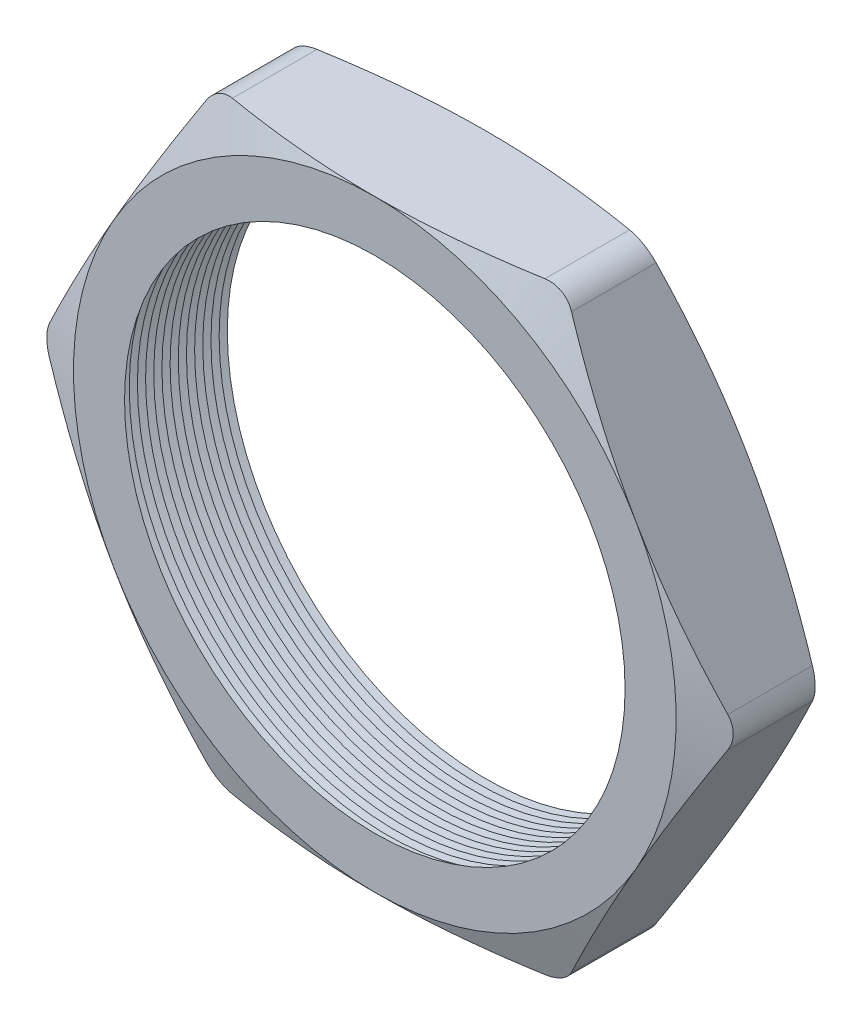
SolidWorks part; units mm, degrees
ref_plane "Front Plane" through (0, 0, 0) normal (0, 0, 1) x (1, 0, 0)
ref_plane "Top Plane" through (0, 0, 0) normal (0, 1, 0) x (1, 0, 0)
ref_plane "Right Plane" through (0, 0, 0) normal (1, 0, 0) x (0, 0, -1)
sketch "Sketch1" plane through (0, 0, 0) normal (0, 0, 1) x (1, 0, 0)
  line L1 (-8.6522, 0) -> (-4.3261, -7.493)
  line L2 (-4.3261, -7.493) -> (4.3261, -7.493)
  line L3 (4.3261, -7.493) -> (8.6522, 0)
  line L4 (8.6522, 0) -> (4.3261, 7.493)
  line L5 (4.3261, 7.493) -> (-4.3261, 7.493)
  line L6 (-4.3261, 7.493) -> (-8.6522, 0)
  circle A0 centre (0, 0) radius 7.493 construction
  circle A1 centre (0, 0) radius 6.223
  dimension "TS" = 12.446
  dimension "H" = 14.986
extrude "Extrude1" add sketch "Sketch1" along normal blind 2.794
fillet "Fillet1" radius 0.762 6 edges at (-4.3261, 7.493, 1.397) (-8.6522, 0, 1.397) (-4.3261, -7.493, 1.397) (4.3261, -7.493, 1.397) (8.6522, 0, 1.397) (4.3261, 7.493, 1.397)
sketch "Sketch2" plane through (0, 0, 2.794) normal (0, 0, 1) x (1, 0, 0)
  line L0 (3.8861, 7.493) -> (-3.8861, 7.493) construction
  circle A0 centre (0, 0) radius 7.493
extrude "Cut-Extrude1" cut sketch "Sketch2" against normal through all draft 70 flip side to cut
sketch "Sketch3" plane through (0, 0, 0) normal (0, 0, -1) x (-1, 0, 0)
  circle A0 centre (0, 0) radius 7.493
extrude "Cut-Extrude2" cut sketch "Sketch3" against normal through all draft 70 flip side to cut
sketch "Sketch4" plane through (0, 0, 0) normal (0, 1, 0) x (1, 0, 0)
  line L0 (-6.223, -2.794) -> (-6.223, -2.3541)
  line L2 (-6.223, -2.3541) -> (-6.604, -2.574)
  line L3 (-6.604, -2.574) -> (-6.223, -2.794)
  line L5 (-6.223, 0) -> (-6.223, -2.794) construction
  line L6 (-6.223, -2.794) -> (6.223, -2.794) construction
  dimension "D1" = 60
  dimension "D2" = 60
  dimension "D3" = 0.381
revolve "Cut-Revolve1" cut sketch "Sketch4" angle 360 about axis through (0, 0, 2.794) along (0, 0, -1)
pattern_linear "LPattern1" count 14 spacing 0.2032 along (0, 0, -1) of "Cut-Revolve1"
